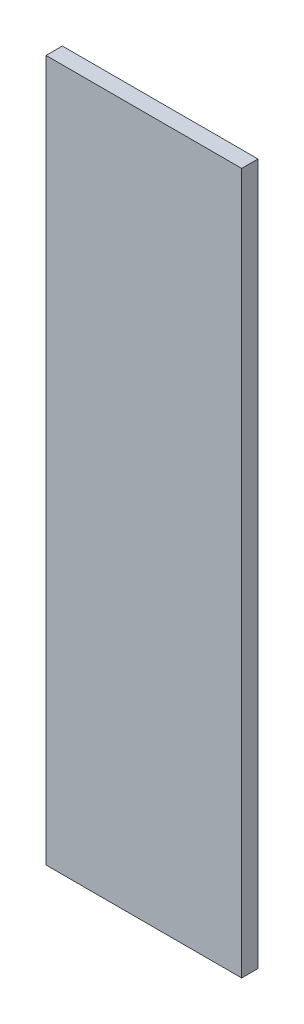
SolidWorks part; units mm, degrees
ref_plane "Front Plane" through (0, 0, 0) normal (0, 0, 1) x (1, 0, 0)
ref_plane "Top Plane" through (0, 0, 0) normal (0, 1, 0) x (1, 0, 0)
ref_plane "Right Plane" through (0, 0, 0) normal (1, 0, 0) x (0, 0, -1)
sketch "Sketch1" plane through (0, 0, 0) normal (0, 0, 1) x (1, 0, 0)
  line L1 (0, 222.25) -> (152.4, 222.25)
  line L2 (0, 222.25) -> (0, -323.85)
  line L3 (0, -323.85) -> (152.4, -323.85)
  line L4 (152.4, 222.25) -> (152.4, -323.85)
  dimension "D1" = 546.1
  dimension "D2" = 152.4
extrude "Boss-Extrude1" add sketch "Sketch1" along normal blind 12.7
